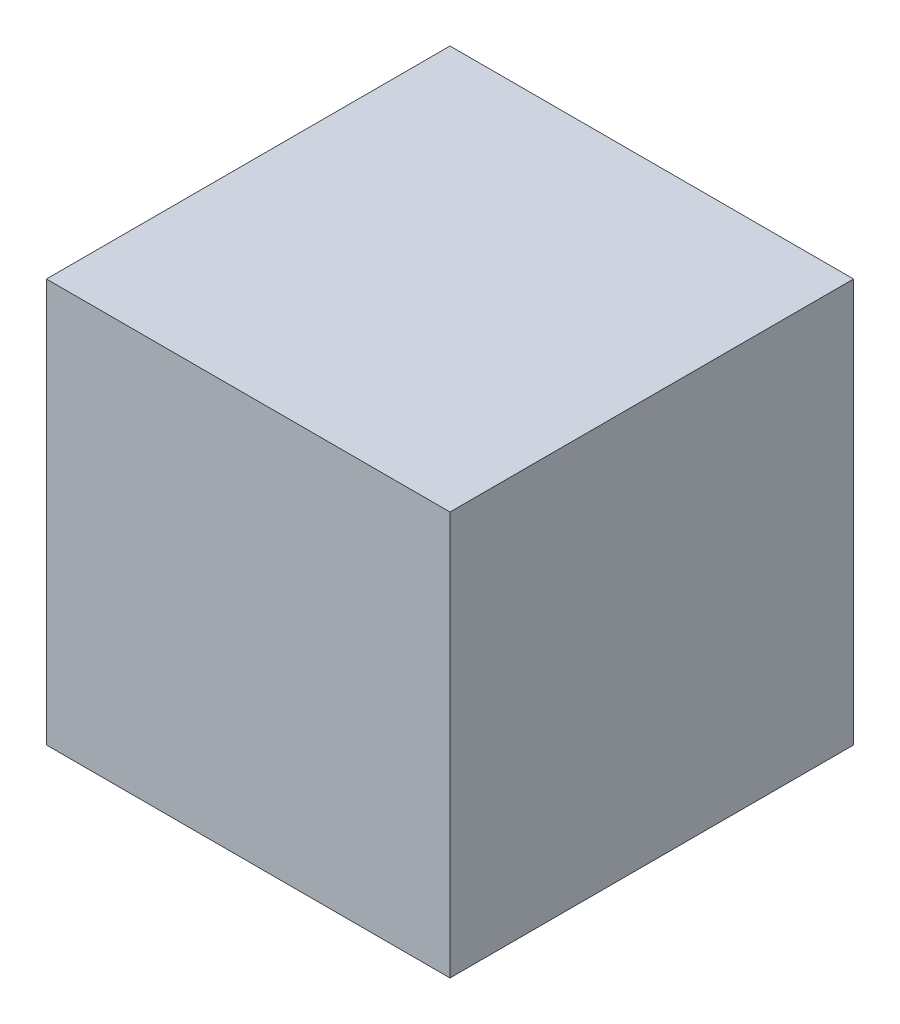
SolidWorks part; units mm, degrees
ref_plane "Front Plane" through (0, 0, 0) normal (0, 0, 1) x (1, 0, 0)
ref_plane "Top Plane" through (0, 0, 0) normal (0, 1, 0) x (1, 0, 0)
ref_plane "Right Plane" through (0, 0, 0) normal (1, 0, 0) x (0, 0, -1)
sketch "Sketch1" plane through (0, 0, 0) normal (0, 0, 1) x (1, 0, 0)
  line L1 (-30, 30) -> (30, 30)
  line L2 (-30, 30) -> (-30, -30)
  line L3 (-30, -30) -> (30, -30)
  line L4 (30, 30) -> (30, -30)
  dimension "D1" = 30
  dimension "D2" = 60
  dimension "D3" = 60
  dimension "D4" = 30
extrude "Boss-Extrude1" add sketch "Sketch1" along normal blind 60
